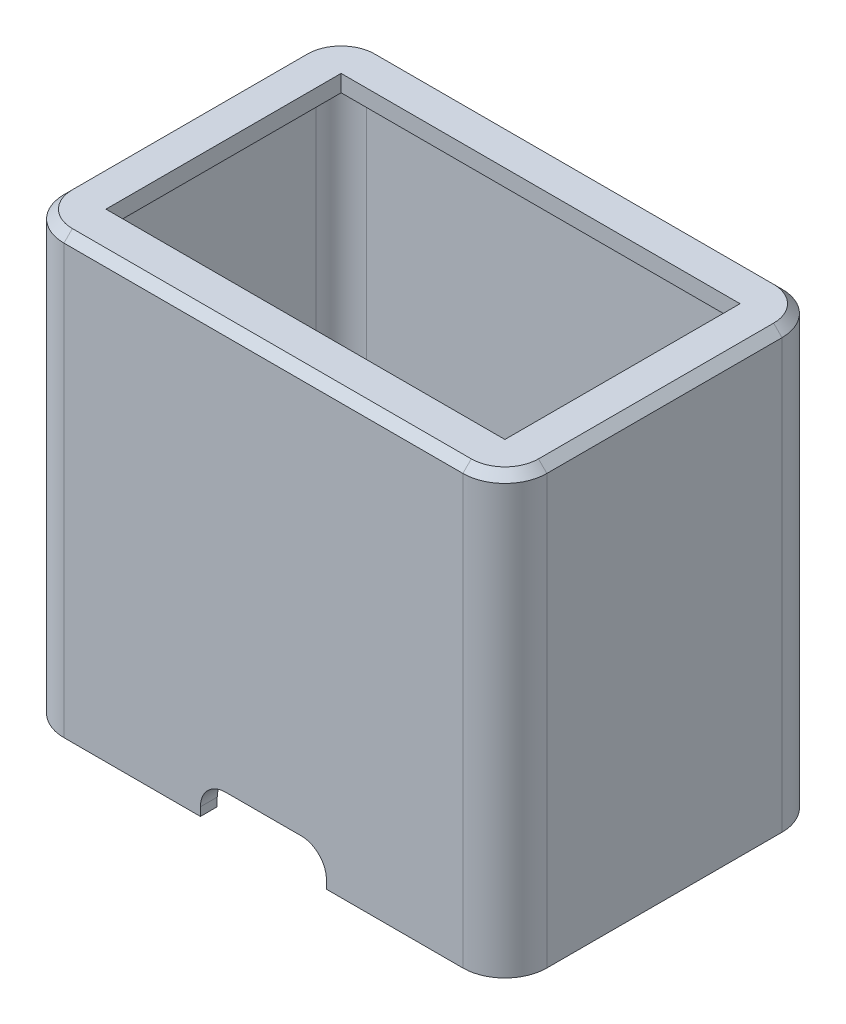
SolidWorks part; units mm, degrees
ref_plane "Front Plane" through (0, 0, 0) normal (0, 0, 1) x (1, 0, 0)
ref_plane "Top Plane" through (0, 0, 0) normal (0, 1, 0) x (1, 0, 0)
ref_plane "Right Plane" through (0, 0, 0) normal (1, 0, 0) x (0, 0, -1)
sketch "Sketch2" plane through (0, 0, 0) normal (0, 1, 0) x (1, 0, 0)
  line L1 (-28.75, 19) -> (28.75, 19)
  line L2 (-28.75, 19) -> (-28.75, -19)
  line L3 (-28.75, -19) -> (28.75, -19)
  line L4 (28.75, 19) -> (28.75, -19)
  line L5 (-28.75, 19) -> (28.75, -19) construction
  line L6 (-28.75, -19) -> (28.75, 19) construction
  line L7 (-23.75, 14) -> (23.75, 14)
  line L8 (-23.75, 14) -> (-23.75, -14)
  line L9 (-23.75, -14) -> (23.75, -14)
  line L10 (23.75, 14) -> (23.75, -14)
  line L11 (-23.75, 14) -> (23.75, -14) construction
  line L12 (-23.75, -14) -> (23.75, 14) construction
  point P0 (0, 0)
  point P5 (0, 0)
  dimension "D1" = 5
  dimension "D2" = 47.5
  dimension "D3" = 28
  dimension "D4" = 5
extrude "Boss-Extrude1" add sketch "Sketch2" along normal blind 2
sketch "Sketch3" plane through (0, 0, 0) normal (0, -1, 0) x (1, 0, 0)
  line L8 (26.75, -17) -> (26.75, 17)
  line L9 (26.75, 17) -> (-26.75, 17)
  line L10 (-26.75, 17) -> (-26.75, -17)
  line L11 (-26.75, -17) -> (26.75, -17)
  line L12 (26.75, -17) -> (26.75, 17)
  line L13 (26.75, 17) -> (-26.75, 17)
  line L14 (-26.75, 17) -> (-26.75, -17)
  line L15 (-26.75, -17) -> (26.75, -17)
  line L16 (28.75, -19) -> (28.75, 19)
  line L17 (28.75, 19) -> (-28.75, 19)
  line L18 (-28.75, 19) -> (-28.75, -19)
  line L19 (-28.75, -19) -> (28.75, -19)
  line L20 (28.75, -19) -> (28.75, 19)
  line L21 (28.75, 19) -> (-28.75, 19)
  line L22 (-28.75, 19) -> (-28.75, -19)
  line L23 (-28.75, -19) -> (28.75, -19)
  dimension "D1" = 2
  dimension "D2" = 0
extrude "Boss-Extrude2" add sketch "Sketch3" along normal blind 50
fillet "Fillet1" radius 3 4 edges at (-26.75, -25, 17) (26.75, -25, 17) (-26.75, -25, -17) (26.75, -25, -17)
fillet "Fillet2" radius 5 4 edges at (-28.75, -24, 19) (-28.75, -24, -19) (28.75, -24, -19) (28.75, -24, 19)
sketch "Sketch4" plane through (0, 0, 19) normal (0, 0, 1) x (1, 0, 0)
  line L0 (-7.5, -50) -> (-7.5, -46)
  line L1 (23.75, -50) -> (-23.75, -50) construction
  line L2 (-7.5, -46) -> (7.5, -46)
  line L3 (7.5, -46) -> (7.5, -50)
  line L4 (7.5, -50) -> (-7.5, -50)
  point P4 (0, -46)
  dimension "D1" = 4
  dimension "D2" = 15
extrude "Cut-Extrude1" cut sketch "Sketch4" against normal up to surface (2 mm away) up to face at (0, -25, 17)
fillet "Fillet3" radius 3 2 edges at (7.5, -46, 18) (-7.5, -46, 18)
chamfer "Chamfer1" distance 1 angle 45 8 edges at (-27.2855, 2, -17.5355) (-28.75, 2, 0) (0, 2, -19) (-27.2855, 2, 17.5355) (27.2855, 2, -17.5355) (0, 2, 19) (28.75, 2, 0) (27.2855, 2, 17.5355)
sketch "Sketch6" plane through (0, -50, 0) normal (0, -1, 0) x (1, 0, 0)
  line L0 (-28.75, 14) -> (-28.75, -14) construction
  line L1 (-28.75, 4) -> (-13.75, 4)
  line L2 (-28.75, 4) -> (-28.75, -4)
  line L3 (-28.75, -4) -> (-13.75, -4)
  line L4 (-13.75, 4) -> (-13.75, -4)
  line L5 (-13.75, 0) -> (-26.75, 0) construction
  line L6 (-26.75, 14) -> (-26.75, -14) construction
  line L7 (-23.75, -14) -> (-23.75, 14) construction
  circle A0 centre (-18.75, 0) radius 1.75
  point P6 (-28.75, 0)
  dimension "D3" = 5
  dimension "D4" = 3.5
  dimension "D1" = 15
  dimension "D2" = 8
extrude "Boss-Extrude3" add sketch "Sketch6" against normal blind 2.5
mirror "Mirror1" about plane through (0, 0, 0) normal (1, 0, 0) of "Boss-Extrude3"
fillet "Fillet4" radius 3 8 edges at (-13.75, -48.75, -4) (-26.75, -48.75, -4) (-26.75, -48.75, 4) (-13.75, -48.75, 4) (26.75, -48.75, -4) (13.75, -48.75, -4) (13.75, -48.75, 4) (26.75, -48.75, 4)
